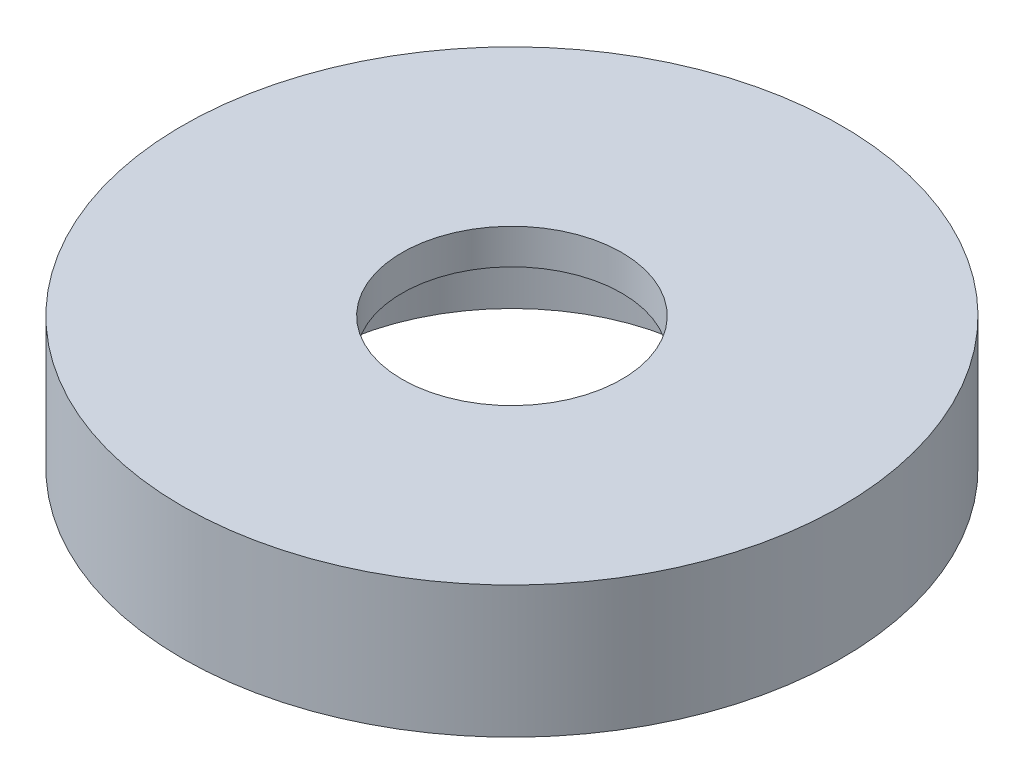
SolidWorks part; units mm, degrees
ref_plane "Front Plane" through (0, 0, 0) normal (0, 0, 1) x (1, 0, 0)
ref_plane "Top Plane" through (0, 0, 0) normal (0, 1, 0) x (1, 0, 0)
ref_plane "Right Plane" through (0, 0, 0) normal (1, 0, 0) x (0, 0, -1)
sketch "Sketch1" plane through (0, 0, 0) normal (0, 1, 0) x (1, 0, 0)
  circle A0 centre (0, 0) radius 95.25
  dimension "D1" = 190.5
extrude "Boss-Extrude1" add sketch "Sketch1" along normal mid plane 38.1
sketch "Sketch2" plane through (0, 19.05, 0) normal (0, 1, 0) x (1, 0, 0)
  circle A0 centre (0, 0) radius 31.75
  dimension "D1" = 63.5
extrude "Cut-Extrude1" cut sketch "Sketch2" against normal blind 10.16
sketch "Sketch3" plane through (0, -19.05, 0) normal (0, -1, 0) x (1, 0, 0)
  circle A0 centre (0, 0) radius 56.515
  dimension "D1" = 113.03
extrude "Cut-Extrude2" cut sketch "Sketch3" against normal up to surface (27.94 mm away) contours A0 up to face at (0, 8.89, 31.75)
sketch "Sketch4" plane through (0, -19.05, 0) normal (0, -1, 0) x (1, 0, 0)
  circle A0 centre (0, 0) radius 76.2 construction
  circle A1 centre (0, 0) radius 95.25 construction
  circle A2 centre (-76.2, 0) radius 3.175
  dimension "D1" = 19.05
  dimension "D2" = 6.35
extrude "Cut-Extrude3" cut sketch "Sketch4" against normal blind 19.05
pattern_circular "CirPattern1" count 3 over 360 about axis through (0, 0, 0) along (0, 1, 0) of "Cut-Extrude3"
